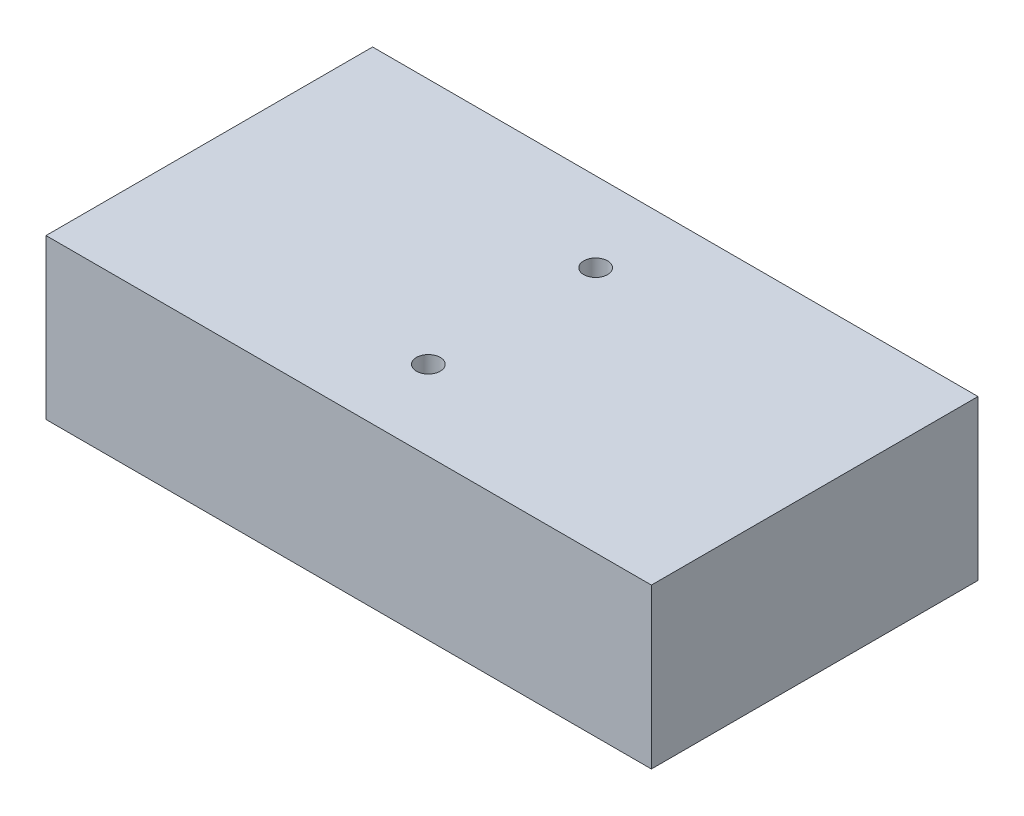
SolidWorks part; units mm, degrees
ref_plane "Front Plane" through (0, 0, 0) normal (0, 0, 1) x (1, 0, 0)
ref_plane "Top Plane" through (0, 0, 0) normal (0, 1, 0) x (1, 0, 0)
ref_plane "Right Plane" through (0, 0, 0) normal (1, 0, 0) x (0, 0, -1)
sketch "Sketch1" plane through (0, 0, 0) normal (0, 1, 0) x (1, 0, 0)
  line L0 (-32.5431, -9.2389) -> (43.4569, -9.2389) construction
  line L1 (-32.5431, 11.2611) -> (43.4569, 11.2611)
  line L2 (-32.5431, 11.2611) -> (-32.5431, -29.7389)
  line L3 (-32.5431, -29.7389) -> (43.4569, -29.7389)
  line L4 (43.4569, 11.2611) -> (43.4569, -29.7389)
  line L5 (5.4569, 1.2611) -> (5.4569, -9.2389) construction
  line L6 (5.4569, -9.2389) -> (5.4569, -19.7389) construction
  circle A0 centre (5.4569, 1.2611) radius 1.5
  circle A1 centre (5.4569, -19.7389) radius 1.5
  dimension "D4" = 3
  dimension "D1" = 76
  dimension "D2" = 41
  dimension "D3" = 10.5
extrude "Boss-Extrude1" add sketch "Sketch1" along normal blind 20
